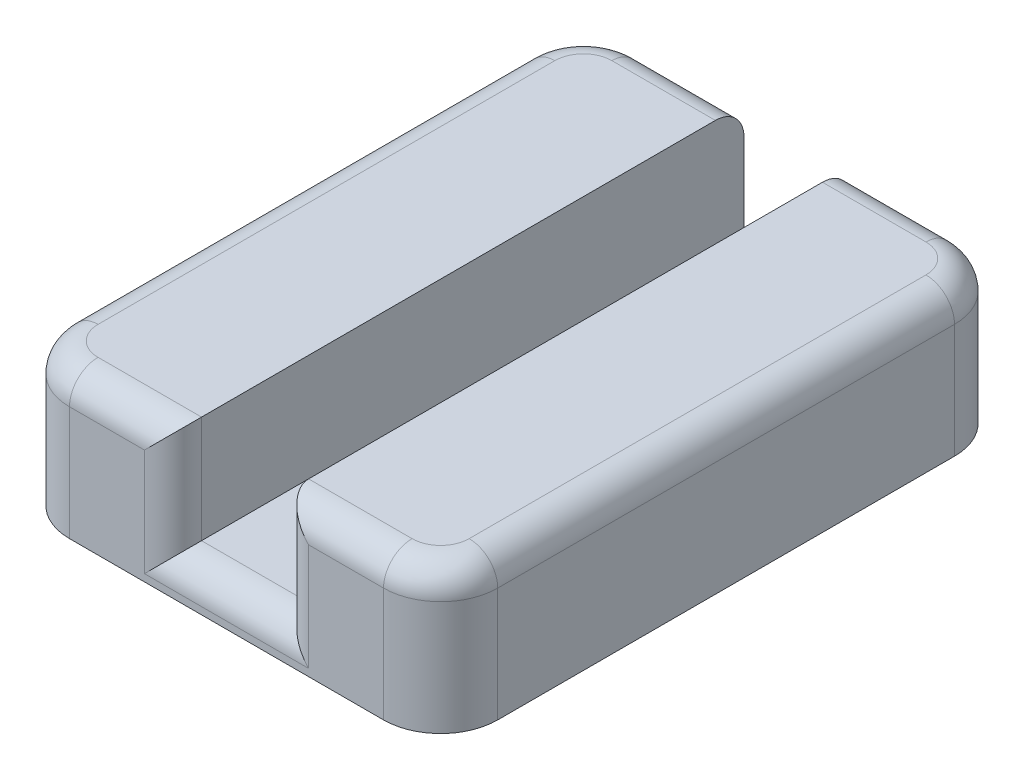
SolidWorks part; units mm, degrees
ref_plane "Front Plane" through (0, 0, 0) normal (0, 0, 1) x (1, 0, 0)
ref_plane "Top Plane" through (0, 0, 0) normal (0, 1, 0) x (1, 0, 0)
ref_plane "Right Plane" through (0, 0, 0) normal (1, 0, 0) x (0, 0, -1)
sketch "Sketch1" plane through (0, 0, 0) normal (0, 1, 0) x (1, 0, 0)
  line L0 (11.9062, 25.4) -> (16.51, 25.4)
  line L1 (2.54, 0) -> (16.51, 0)
  line L2 (0, 2.54) -> (0, 22.86)
  line L3 (2.54, 25.4) -> (7.1437, 25.4)
  line L4 (19.05, 2.54) -> (19.05, 22.86)
  line L6 (7.1437, 25.4) -> (7.1438, 19.05)
  line L7 (7.1438, 19.05) -> (11.9062, 19.05)
  line L8 (11.9062, 25.4) -> (11.9062, 19.05)
  arc A0 (16.51, 0) -> (19.05, 2.54) centre (16.51, 2.54) ccw
  arc A1 (2.54, 0) -> (0, 2.54) centre (2.54, 2.54) cw
  arc A2 (16.51, 25.4) -> (19.05, 22.86) centre (16.51, 22.86) cw
  arc A3 (0, 22.86) -> (2.54, 25.4) centre (2.54, 22.86) cw
  point P9 (7.1437, 21.6568)
  point P12 (19.05, 0)
  point P15 (0, 0)
  point P18 (19.05, 25.4)
  point P21 (0, 25.4)
  dimension "D7" = 2.54
  dimension "D1" = 4.7625
  dimension "D2" = 19.05
  dimension "D3" = 7.1437
  dimension "D4" = 7.1437
  dimension "D5" = 6.35
  dimension "D6" = 25.4
extrude "Boss-Extrude1" add sketch "Sketch1" along normal blind 6.35 contours L2 A3 L3 L6 L7 L8 L0 A2 L4 A0 L1 A1
sketch "Sketch2" plane through (0, 6.35, 0) normal (0, 1, 0) x (1, 0, 0)
  line L0 (2.54, 0) -> (16.51, 0) construction
  line L1 (7.1438, 19.05) -> (11.9062, 19.05)
  line L2 (7.1438, 19.05) -> (7.1438, 0)
  line L3 (7.1438, 0) -> (11.9063, 0)
  line L4 (11.9062, 19.05) -> (11.9063, 0)
  line L5 (11.9062, 25.4) -> (11.9062, 19.05) construction
extrude "Cut-Extrude1" cut sketch "Sketch2" against normal blind 4.7625
fillet "Fillet1" radius 1.27 14 edges at (14.2081, 6.35, -25.4) (18.3061, 6.35, -24.6561) (19.05, 6.35, -12.7) (18.3061, 6.35, -0.7439) (4.8419, 6.35, -25.4) (0.7439, 6.35, -24.6561) (0, 6.35, -12.7) (0.7439, 6.35, -0.7439) (9.525, 1.5875, 0) (9.525, 1.5875, -19.05) (14.2081, 6.35, 0) (11.9062, 3.9688, 0) (7.1438, 3.9688, 0) (4.8419, 6.35, 0)
